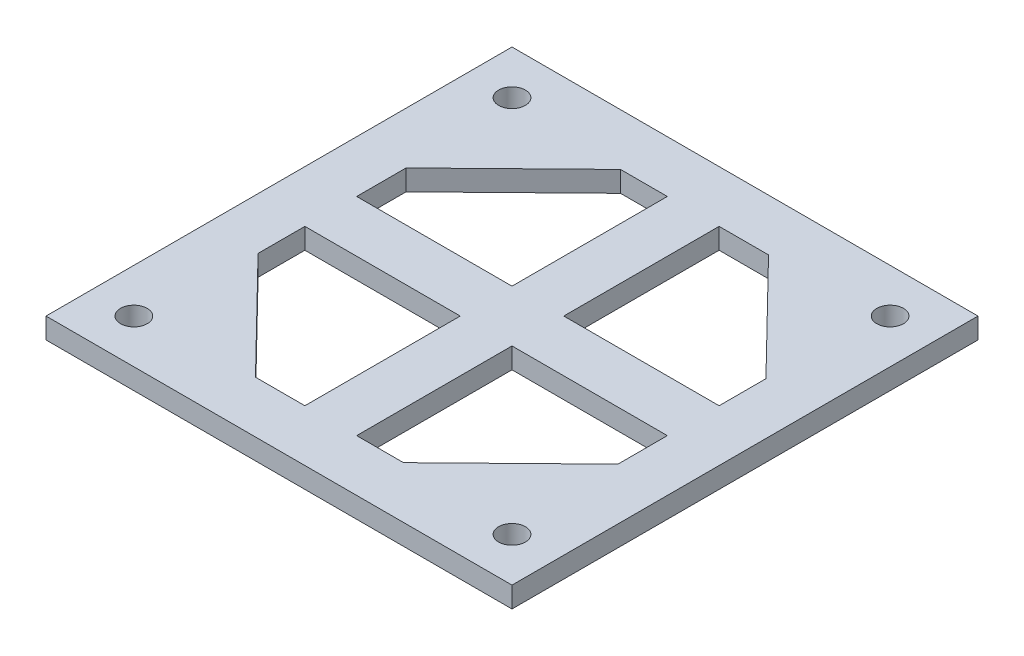
SolidWorks part; units mm, degrees
material "Thornel VCB-20 Carbon Cloth"
ref_plane "Front Plane" through (0, 0, 0) normal (0, 0, 1) x (1, 0, 0)
ref_plane "Top Plane" through (0, 0, 0) normal (0, 1, 0) x (1, 0, 0)
ref_plane "Right Plane" through (0, 0, 0) normal (1, 0, 0) x (0, 0, -1)
sketch "Sketch2" plane through (0, 0, 0) normal (0, 1, 0) x (1, 0, 0)
  line L1 (-22.5, 22.5) -> (22.5, 22.5)
  line L2 (-22.5, 22.5) -> (-22.5, -22.5)
  line L3 (-22.5, -22.5) -> (22.5, -22.5)
  line L4 (22.5, 22.5) -> (22.5, -22.5)
  line L5 (-22.5, 22.5) -> (22.5, -22.5) construction
  line L6 (-22.5, -22.5) -> (22.5, 22.5) construction
  point P0 (0, 0)
  dimension "D1" = 45
  dimension "D2" = 45
extrude "Boss-Extrude1" add sketch "Sketch2" along normal blind 2
sketch "Sketch4" plane through (0, 0, 0) normal (0, -1, 0) x (1, 0, 0)
  line L1 (-22.5, 22.5) -> (22.5, 22.5) construction
  line L2 (22.5, 22.5) -> (22.5, -22.5) construction
  line L5 (0, 0) -> (1.77, 0) construction
  line L6 (7.0218, 17.5) -> (17.5, 7.2717)
  line L7 (17.5, 7.2717) -> (17.5, 2.5)
  line L8 (17.5, 2.5) -> (2.5, 2.5)
  line L9 (2.5, 2.5) -> (2.5, 17.5)
  line L10 (2.5, 17.5) -> (7.0218, 17.5)
  line L11 (0, -22.5) -> (0, 22.5) construction
  line L12 (22.5, -22.5) -> (-22.5, -22.5) construction
  line L13 (-22.5, 0) -> (22.5, 0) construction
  line L14 (-22.5, -22.5) -> (-22.5, 22.5) construction
  dimension "D2" = 5
  dimension "D3" = 5
  dimension "D4" = 2.5
  dimension "D5" = 2.5
extrude "Cut-Extrude1" cut sketch "Sketch4" against normal up to surface (2 mm away) up to face at (0, 2, 0)
sketch "Sketch7" plane through (0, 0, 0) normal (0, -1, 0) x (1, 0, 0)
  line L0 (-22.5, -22.5) -> (22.5, 22.5) construction
  circle A0 centre (18.2574, 18.2574) radius 1.2892
  dimension "D1" = 6
extrude "Cut-Extrude2" cut sketch "Sketch7" against normal up to next (2 mm away)
sketch "Sketch5" plane through (0, 0, 0) normal (1, 0, 0) x (0, 0, -1)
  line L0 (0, -0.174) -> (0, 0.9435) construction
pattern_circular "CirPattern1" count 4 over 360 about axis through (0, 0, 0) along (0, 1, 0) of "Cut-Extrude1", "Cut-Extrude2"
